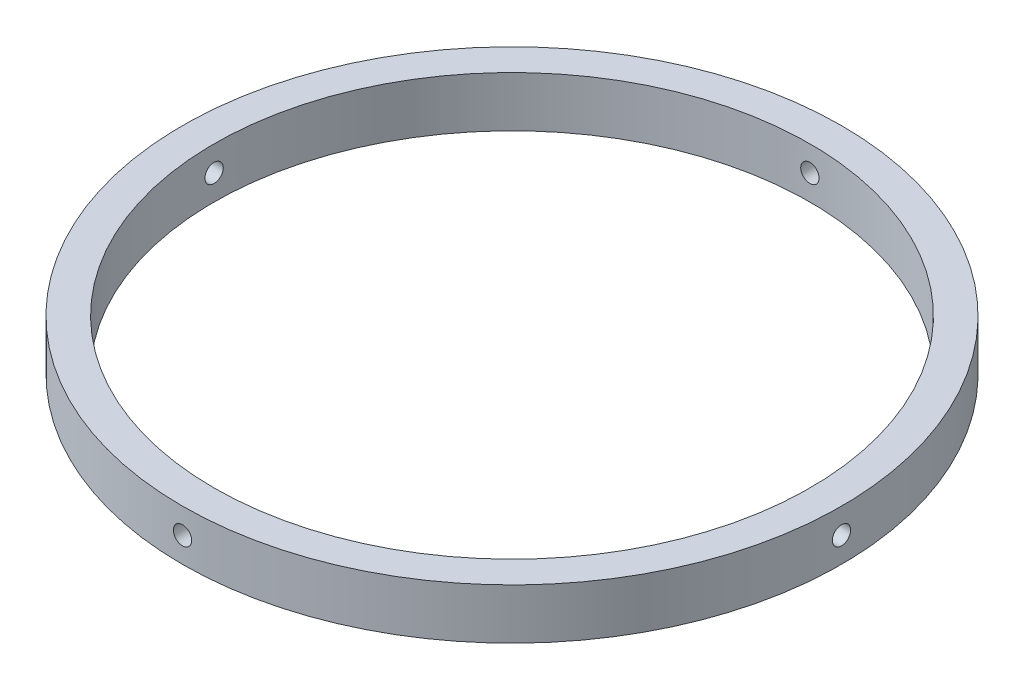
SolidWorks part; units mm, degrees
ref_plane "Front Plane" through (0, 0, 0) normal (0, 0, 1) x (1, 0, 0)
ref_plane "Top Plane" through (0, 0, 0) normal (0, 1, 0) x (1, 0, 0)
ref_plane "Right Plane" through (0, 0, 0) normal (1, 0, 0) x (0, 0, -1)
sketch "Sketch1" plane through (0, 0, 0) normal (0, 1, 0) x (1, 0, 0)
  circle A0 centre (0, 0) radius 47.25
  circle A1 centre (0, 0) radius 52.25
  dimension "D1" = 94.5
  dimension "D2" = 5
extrude "Boss-Extrude1" add sketch "Sketch1" along normal blind 8
sketch "Sketch2" plane through (0, 0, 0) normal (0, 0, 1) x (1, 0, 0)
  line L0 (0, 0) -> (0, 8) construction
  line L1 (52.25, 8) -> (-52.25, 8) construction
  circle A0 centre (0, 4) radius 1.45
  dimension "D1" = 2.9
extrude "Cut-Extrude1" cut sketch "Sketch2" against normal through all both and the other way through all
sketch "Sketch3" plane through (0, 0, 0) normal (1, 0, 0) x (0, 0, -1)
  line L0 (0, 0) -> (0, 8) construction
  line L1 (52.25, 8) -> (-52.25, 8) construction
  circle A0 centre (0, 4) radius 1.45
  dimension "D1" = 2.9
extrude "Cut-Extrude2" cut sketch "Sketch3" against normal through all both and the other way through all
